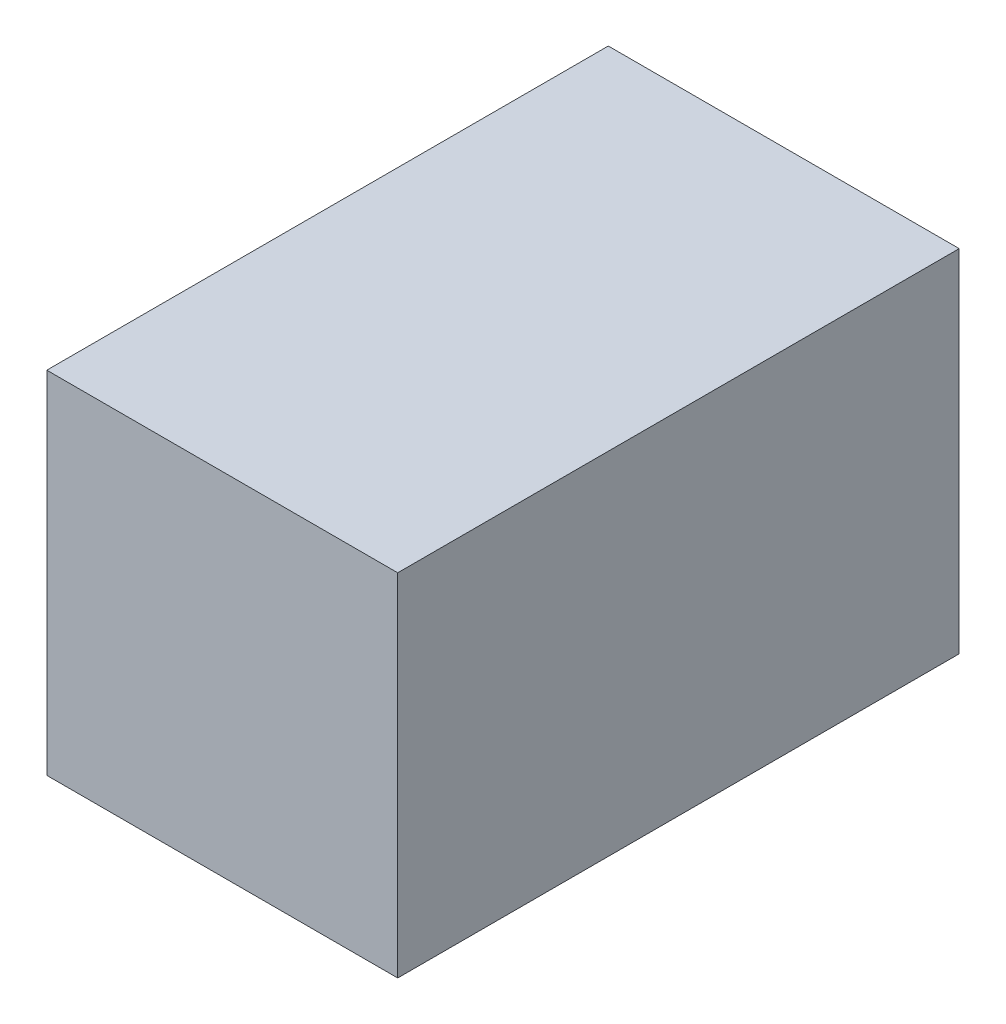
SolidWorks part; units mm, degrees
ref_plane "Front Plane" through (0, 0, 0) normal (0, 0, 1) x (1, 0, 0)
ref_plane "Top Plane" through (0, 0, 0) normal (0, 1, 0) x (1, 0, 0)
ref_plane "Right Plane" through (0, 0, 0) normal (1, 0, 0) x (0, 0, -1)
sketch "BaseS" plane through (0, 0, 0) normal (0, 1, 0) x (1, 0, 0)
  line L1 (-0.5, 0.8) -> (0.5, 0.8)
  line L2 (-0.5, 0.8) -> (-0.5, -0.8)
  line L3 (-0.5, -0.8) -> (0.5, -0.8)
  line L4 (0.5, 0.8) -> (0.5, -0.8)
  line L5 (-0.5, 0.8) -> (0.5, -0.8) construction
  line L6 (-0.5, -0.8) -> (0.5, 0.8) construction
  point P0 (0, 0)
  dimension "Width" = 1
  dimension "Length" = 1.6
extrude "Base" add sketch "BaseS" along normal blind 1
